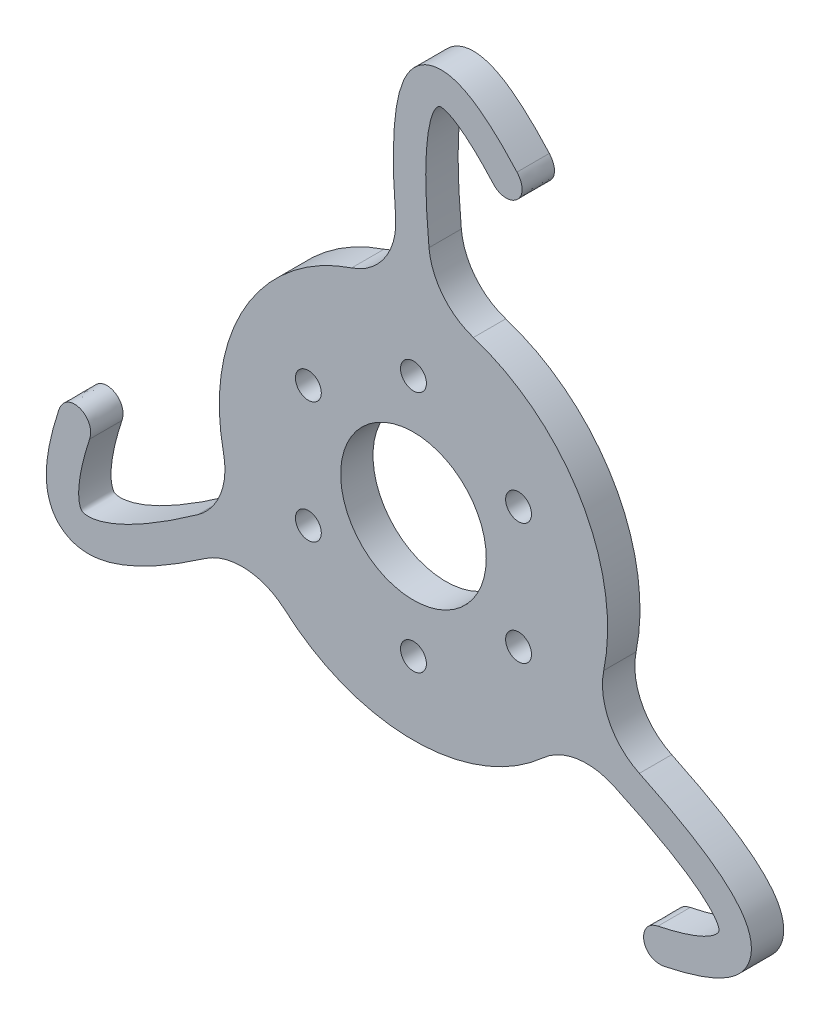
SolidWorks part; units mm, degrees
ref_plane "Front Plane" through (0, 0, 0) normal (0, 0, 1) x (1, 0, 0)
ref_plane "Top Plane" through (0, 0, 0) normal (0, 1, 0) x (1, 0, 0)
ref_plane "Right Plane" through (0, 0, 0) normal (1, 0, 0) x (0, 0, -1)
sketch "Sketch1" plane through (0, 0, 0) normal (0, 0, 1) x (1, 0, 0)
  circle A0 centre (0, 0) radius 38.1
  dimension "D1" = 76.2
extrude "Boss-Extrude1" add sketch "Sketch1" along normal blind 6.35
sketch "Sketch2" plane through (0, 0, 6.35) normal (0, 0, 1) x (1, 0, 0)
  circle A0 centre (0, 0) radius 14.2875
  dimension "D1" = 28.575
extrude "Cut-Extrude1" cut sketch "Sketch2" against normal up to next
sketch "Sketch3" plane through (0, 0, 6.35) normal (0, 0, 1) x (1, 0, 0)
  circle A0 centre (0, 0) radius 23.8125 construction
  circle A1 centre (0, 23.8125) radius 2.54
  circle A2 centre (20.6222, 11.9063) radius 2.54
  circle A3 centre (20.6222, -11.9062) radius 2.54
  circle A4 centre (0, -23.8125) radius 2.54
  circle A5 centre (-20.6222, -11.9063) radius 2.54
  circle A6 centre (-20.6222, 11.9062) radius 2.54
  point P17 (0, 0)
  dimension "D1" = 6
  dimension "D2" = 47.625
  dimension "D3" = 5.08
extrude "Cut-Extrude2" cut sketch "Sketch3" against normal up to next
sketch "Sketch4" plane through (0, 0, 6.35) normal (0, 0, 1) x (1, 0, 0)
  line L0 (1.0175, 36.9352) -> (1.0175, 75.0352) construction
  line L1 (1.0175, 75.0352) -> (13.7175, 75.0352) construction
  line L2 (13.7175, 75.0352) -> (17.9477, 66.5011) construction
  line L3 (4.1648, 37.3535) -> (-2.1298, 36.517)
  circle A0 centre (0, 0) radius 38.1 construction
  circle A2 centre (0, 0) radius 38.1
  spline S0 degree 2 poles (1.0175, 36.9352) (-6.5473, 93.8644) (17.9477, 66.5011) knots 0 0 0 1 1 1 construction
  spline S1 degree 1 poles (4.1648, 37.3535) (15.582, 64.3835) knots 0 0 1 1 construction
  spline S2 degree 3 poles (4.1648, 37.3535) (4.0878, 37.9334) (3.9356, 39.1041) (3.6555, 41.3632) (3.3434, 44.0908) (3.0319, 47.1908) (2.6995, 51.0987) (2.4396, 55.5558) (2.3736, 60.2102) (2.5476, 64.1534) (2.9473, 67.3584) (3.5388, 69.7808) (4.238, 71.3607) (4.8468, 72.058) (5.0935, 72.1694) (5.4279, 72.2509) (6.4683, 72.0535) (8.1294, 71.2246) (9.8955, 69.9458) (11.4914, 68.5668) (12.7723, 67.357) (13.9081, 66.2006) (14.8495, 65.1942) (15.3415, 64.6522) (15.582, 64.3835) knots 0 0 0 0 0.015625 0.03125 0.0625 0.09375 0.125 0.1875 0.25 0.3125 0.375 0.4375 0.5 0.5625 0.625 0.6875 0.75 0.8125 0.875 0.90625 0.9375 0.96875 0.984375 1 1 1 1
  spline S3 degree 1 poles (-2.1298, 36.517) (20.3133, 68.6188) knots 0 0 1 1 construction
  spline S4 degree 3 poles (-2.1298, 36.517) (-2.2085, 37.109) (-2.3638, 38.3035) (-2.6502, 40.6137) (-2.9702, 43.4096) (-3.2909, 46.601) (-3.635, 50.6452) (-3.9074, 55.3042) (-3.9794, 60.2724) (-3.7903, 64.6347) (-3.3261, 68.4181) (-2.5528, 71.6671) (-1.3861, 74.4414) (0.3717, 76.7814) (2.9927, 78.3901) (6.0269, 78.7117) (8.8561, 77.995) (11.5655, 76.5928) (13.8587, 74.915) (15.7612, 73.2697) (17.228, 71.8833) (18.4905, 70.5974) (19.5212, 69.4955) (20.0526, 68.91) (20.3133, 68.6188) knots 0 0 0 0 0.015625 0.03125 0.0625 0.09375 0.125 0.1875 0.25 0.3125 0.375 0.4375 0.5 0.5625 0.625 0.6875 0.75 0.8125 0.875 0.90625 0.9375 0.96875 0.984375 1 1 1 1
  spline S5 degree 3 poles (15.582, 64.3835) (18.5216, 61.109) (23.4646, 64.8994) (20.3133, 68.6188) knots 0 0 0 0 1 1 1 1
  circle M12 centre (0, 0) radius 38.1
  dimension "D1" = 38.1
  dimension "D2" = 12.7
  dimension "D3" = 9.525
  dimension "D4" = 3.175
  dimension "D5" = 3.175
extrude "Boss-Extrude2" add sketch "Sketch4" against normal up to surface (6.35 mm away) contours S2 S5 S4 M12 up to face at (23.1622, 11.9063, 0)
fillet "Fillet1" radius 12.7 2 edges at (4.0954, 37.8792, 3.175) (-2.327, 38.0289, 3.175)
ref_axis "Axis1" through (0, 0, -43.9453) along (0, 0, 1)
pattern_circular "CirPattern1" count 3 over 360 about axis through (0, 0, -43.9453) along (0, 0, 1) of "Boss-Extrude2", "Fillet1"
sketch "Sketch5" plane through (0, 0, 6.35) normal (0, 0, 1) x (1, 0, 0)
  line L0 (0, 0) -> (79.375, 0) construction
  circle A0 centre (0, 0) radius 79.375 construction
  dimension "D1" = 158.75
